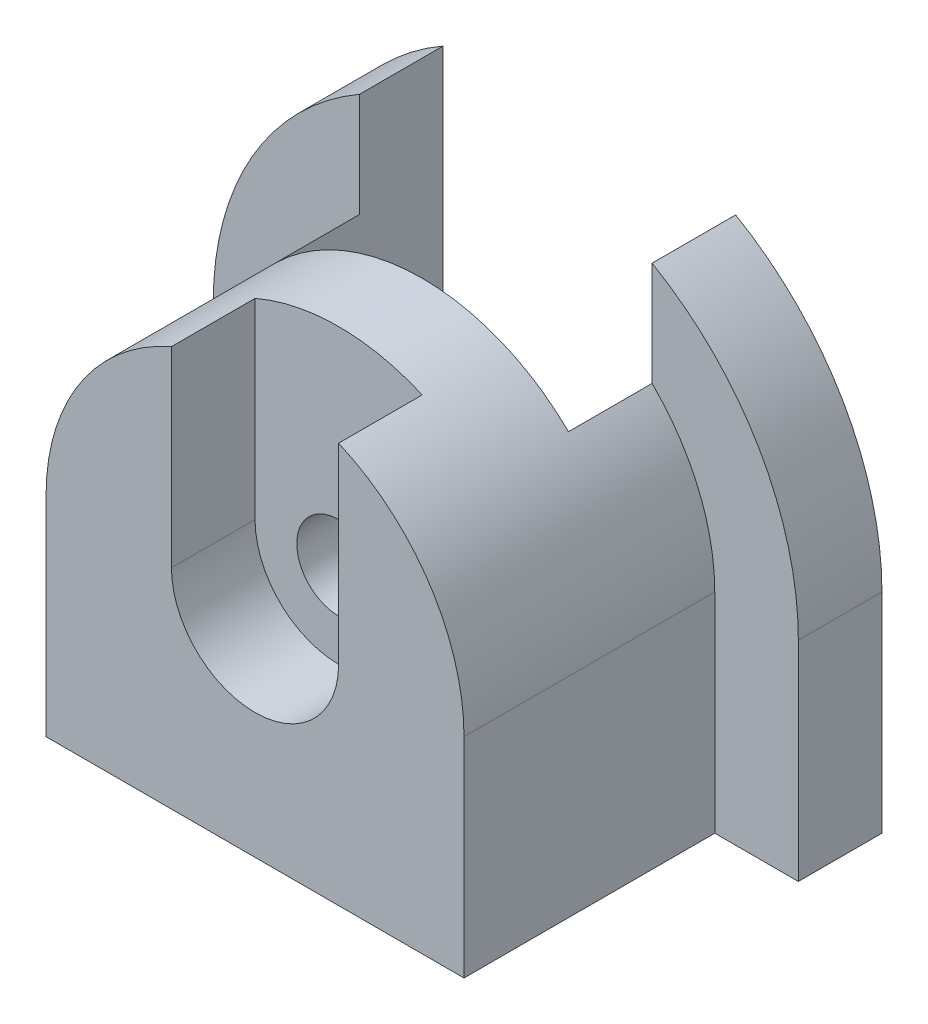
SolidWorks part; units mm, degrees
ref_plane "Front Plane" through (0, 0, 0) normal (0, 0, 1) x (1, 0, 0)
ref_plane "Top Plane" through (0, 0, 0) normal (0, 1, 0) x (1, 0, 0)
ref_plane "Right Plane" through (0, 0, 0) normal (1, 0, 0) x (0, 0, -1)
sketch "Sketch1" plane through (0, 0, 0) normal (0, 0, 1) x (1, 0, 0)
  line L0 (-50, 0) -> (-50, -50)
  line L1 (-50, -50) -> (50, -50)
  line L2 (50, -50) -> (50, 0)
  arc A0 (-50, 0) -> (50, 0) centre (0, 0) cw
  dimension "D1" = 50
  dimension "D2" = 100
  dimension "D3" = 0
  dimension "D4" = 50
extrude "Boss-Extrude1" add sketch "Sketch1" along normal blind 60 contours A0 L0 L1 L2
sketch "Sketch2" plane through (0, 0, 60) normal (0, 0, 1) x (1, 0, 0)
  circle A0 centre (0, 0) radius 10
  dimension "D1" = 20
  dimension "D2" = 50
  dimension "D3" = 50
extrude "Cut-Extrude1" cut sketch "Sketch2" against normal blind 60
sketch "Sketch3" plane through (0, 0, 60) normal (0, 0, 1) x (1, 0, 0)
  line L0 (-20, 0) -> (-20, 45.8258)
  line L1 (20, 0) -> (20, 45.8258)
  arc A0 (20, 0) -> (-20, 0) centre (0, 0) cw
  arc A1 (50, 0) -> (-50, 0) centre (0, 0) ccw construction
  arc A2 (-20, 45.8258) -> (20, 45.8258) centre (0, 0) cw
  dimension "D1" = 20
extrude "Cut-Extrude2" cut sketch "Sketch3" against normal blind 20
sketch "Sketch6" plane through (0, 0, 0) normal (0, 0, -1) x (-1, 0, 0)
  line L0 (-35, 0) -> (-35, 35.7071)
  line L1 (35, 0) -> (35, 35.7071)
  arc A0 (35, 0) -> (-35, 0) centre (0, 0) cw
  arc A1 (50, 0) -> (-50, 0) centre (0, 0) ccw construction
  arc A2 (35, 35.7071) -> (-35, 35.7071) centre (0, 0) ccw
  circle M1 centre (0, 0) radius 10
  arc M2 (50, 0) -> (-50, 0) centre (0, 0) ccw
  dimension "D1" = 35
extrude "Cut-Extrude6" cut sketch "Sketch6" against normal blind 20 contours A0 L1 L0 M2 M1
sketch "Sketch7" plane through (0, 0, 0) normal (0, 0, -1) x (-1, 0, 0)
  line L0 (35, 60.6218) -> (35, -50)
  line L1 (50, -50) -> (-50, -50) construction
  line L2 (35, -50) -> (50, -50)
  line L3 (50, -50) -> (50, 0)
  line L4 (50, 0) -> (50, -50) construction
  line L5 (-35, 60.6218) -> (-35, -50)
  line L6 (-35, -50) -> (-50, -50)
  line L7 (-50, -50) -> (-50, 0)
  line L8 (70, 0) -> (70, -50)
  line L9 (50, -50) -> (70, -50)
  line L10 (-50, -50) -> (-70, -50)
  line L11 (-70, -50) -> (-70, 0)
  arc A0 (70, 0) -> (35, 60.6218) centre (0, 0) ccw
  arc A1 (-70, 0) -> (-35, 60.6218) centre (0, 0) cw
  arc A2 (50, 0) -> (35, 35.7071) centre (0, 0) ccw construction
  arc A3 (-50, 0) -> (-35, 35.7071) centre (0, 0) cw
  arc A4 (-35, 35.7071) -> (-50, 0) centre (0, 0) ccw construction
  arc A5 (50, 0) -> (35, 35.7071) centre (0, 0) ccw
  line M1 (-35, 0) -> (-35, 35.7071)
  arc M2 (-35, 35.7071) -> (-50, 0) centre (0, 0) ccw
  line M3 (-50, 0) -> (-50, -50)
  line M4 (-50, -50) -> (50, -50)
  line M5 (50, -50) -> (50, 0)
  arc M6 (50, 0) -> (35, 35.7071) centre (0, 0) ccw
  line M7 (35, 35.7071) -> (35, 0)
  dimension "D5" = 50
  dimension "D1" = 70
  dimension "D2" = 70
  dimension "D3" = 50
  dimension "D4" = 50
extrude "Boss-Extrude2" add sketch "Sketch7" along normal blind 20 contours A1 L11 L10 L5 M3 M2 | L5 M1 M2 M3 M4 | L0 M7 M4 M5 M6 | L8 A0 L0 L9 M6 M5
sketch "Sketch8" plane through (0, 0, 0) normal (0, 0, -1) x (-1, 0, 0)
  line L0 (-35, -50) -> (-35, 0)
  line L1 (-35, -50) -> (35, -50)
  line L2 (35, -50) -> (35, 0)
  arc A0 (-35, 0) -> (35, 0) centre (0, 0) ccw construction
  arc A1 (35, 0) -> (-35, 0) centre (0, 0) cw
  line M1 (35, -50) -> (35, 0)
  arc M2 (35, 0) -> (-35, 0) centre (0, 0) cw
  line M3 (-35, 0) -> (-35, -50)
  line M4 (-35, -50) -> (35, -50)
extrude "Boss-Extrude3" add sketch "Sketch8" along normal blind 20 contours M4 M1 M2 M3
sketch "Sketch9" plane through (0, -50, 0) normal (0, -1, 0) x (1, 0, 0)
  line L0 (-70, -20) -> (70, -20) construction
  line L1 (-20, -20) -> (20, -20)
  line L2 (-20, -20) -> (-20, -10)
  line L3 (-20, -10) -> (20, -10)
  line L4 (20, -20) -> (20, -10)
  dimension "D1" = 10
  dimension "D2" = 40
  dimension "D3" = 50
extrude "Cut-Extrude7" cut sketch "Sketch9" against normal blind 95
